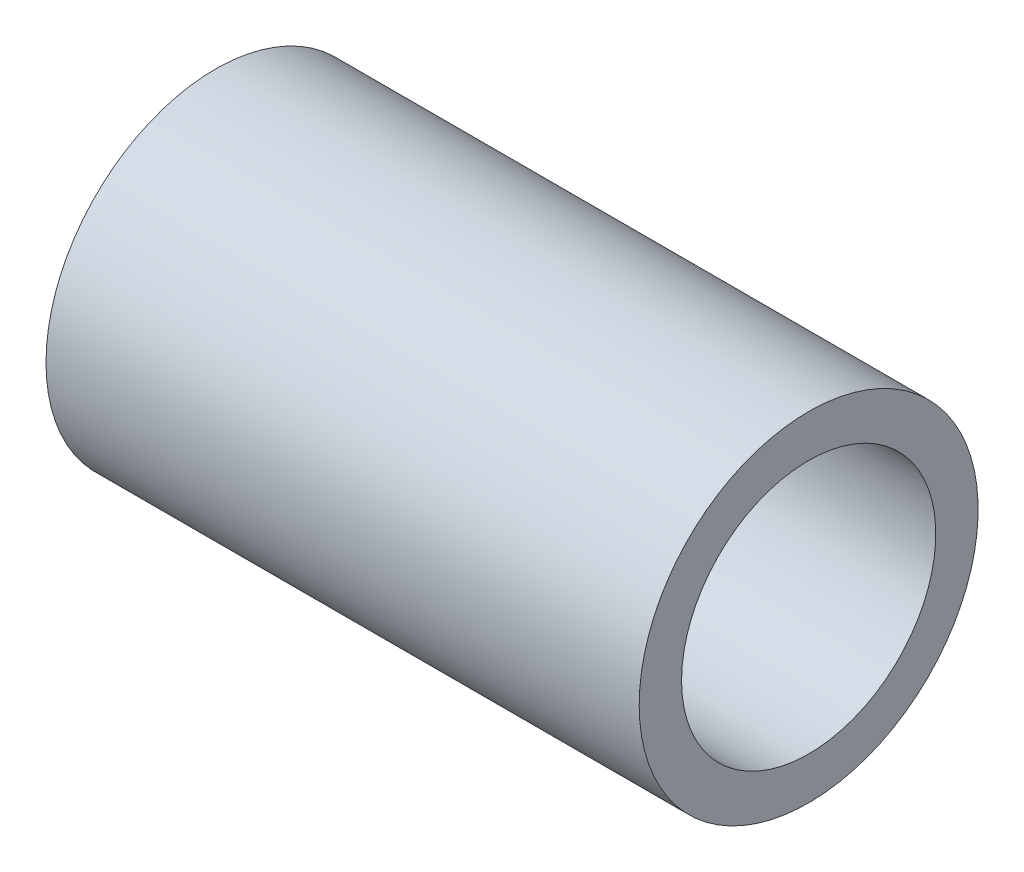
SolidWorks part; units mm, degrees
ref_plane "Front Plane" through (0, 0, 0) normal (0, 0, 1) x (1, 0, 0)
ref_plane "Top Plane" through (0, 0, 0) normal (0, 1, 0) x (1, 0, 0)
ref_plane "Right Plane" through (0, 0, 0) normal (1, 0, 0) x (0, 0, -1)
ref_plane "MidPlane" through (-10.5, 0, 0) normal (1, 0, 0) x (0, 0, -1)
sketch "Sketch1" plane through (0, 0, 0) normal (0, 0, 1) x (1, 0, 0)
  line L0 (-0.9626, 0) -> (0.9703, 0) construction
  line L1 (-3.5, 2) -> (3.5, 2)
  line L2 (-3.5, 2) -> (-3.5, 1.5)
  line L3 (-3.5, 1.5) -> (3.5, 1.5)
  line L4 (3.5, 2) -> (3.5, 1.5)
  point P7 (0, 1.5)
  dimension "D1" = 7
  dimension "D2" = 0.5
  dimension "D3" = 3
revolve "Revolve1" add sketch "Sketch1" angle 360 about L0
